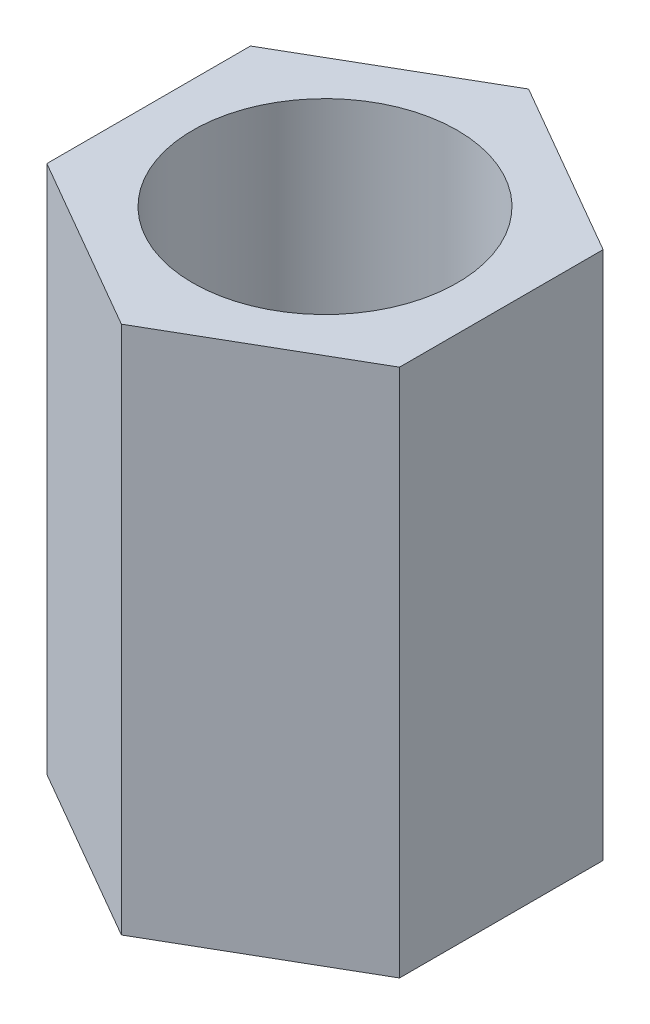
SolidWorks part; units mm, degrees
ref_plane "Front Plane" through (0, 0, 0) normal (0, 0, 1) x (1, 0, 0)
ref_plane "Top Plane" through (0, 0, 0) normal (0, 1, 0) x (1, 0, 0)
ref_plane "Right Plane" through (0, 0, 0) normal (1, 0, 0) x (0, 0, -1)
sketch "Sketch1" plane through (0, 0, 0) normal (0, 1, 0) x (1, 0, 0)
  line L1 (2, 1.1547) -> (0, 2.3094)
  line L2 (0, 2.3094) -> (-2, 1.1547)
  line L3 (-2, 1.1547) -> (-2, -1.1547)
  line L4 (-2, -1.1547) -> (0, -2.3094)
  line L5 (0, -2.3094) -> (2, -1.1547)
  line L6 (2, -1.1547) -> (2, 1.1547)
  circle A0 centre (0, 0) radius 2 construction
  circle A1 centre (0, 0) radius 1.5
  dimension "D1" = 4
  dimension "D2" = 3
extrude "Boss-Extrude1" add sketch "Sketch1" along normal mid plane 6
